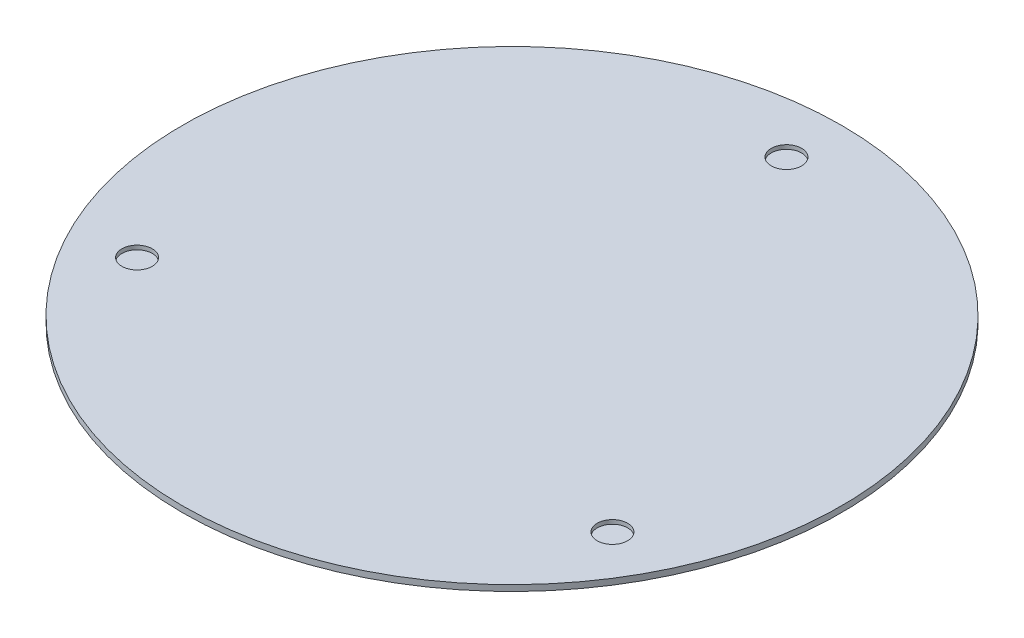
SolidWorks part; units mm, degrees
ref_plane "Front Plane" through (0, 0, 0) normal (0, 0, 1) x (1, 0, 0)
ref_plane "Top Plane" through (0, 0, 0) normal (0, 1, 0) x (1, 0, 0)
ref_plane "Right Plane" through (0, 0, 0) normal (1, 0, 0) x (0, 0, -1)
sketch "Sketch1" plane through (0, 0, 0) normal (0, 1, 0) x (1, 0, 0)
  circle A0 centre (0, 0) radius 165.1
  dimension "D1" = 330.2
extrude "Boss-Extrude1" add sketch "Sketch1" along normal blind 3
sketch "Sketch2" plane through (0, 3, 0) normal (0, 1, 0) x (1, 0, 0)
  line L0 (0, 0) -> (0, 160.2324) construction
  circle A0 centre (0, 137.4902) radius 7.62
  circle A1 centre (0, 0) radius 137.4902 construction
  circle A2 centre (119.07, -68.7451) radius 7.62
  circle A3 centre (-119.07, -68.7451) radius 7.62
  point P12 (0, 0)
  dimension "D1" = 274.9804
  dimension "D2" = 15.24
  dimension "D3" = 3
extrude "Cut-Extrude1" cut sketch "Sketch2" against normal blind 2.032
sketch "Sketch3" plane through (0, 3, 0) normal (0, 1, 0) x (1, 0, 0)
  line L0 (0, 16.1435) -> (0, -16.1435)
  line L1 (-16.1435, 0) -> (16.1435, 0)
  line L2 (-11.4152, 11.4152) -> (11.4152, -11.4152)
  line L3 (11.4152, 11.4152) -> (-11.4152, -11.4152)
  circle A0 centre (0, 0) radius 16.1435
  dimension "D1" = 45
